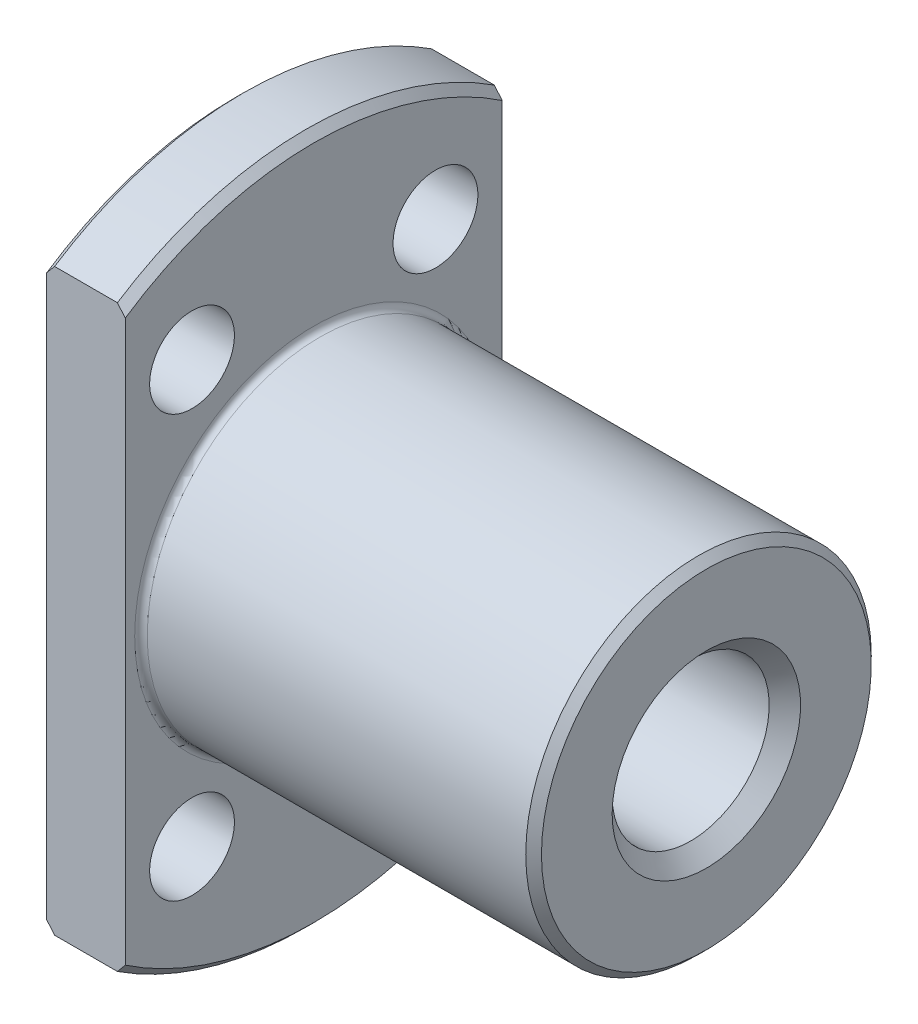
SolidWorks part; units mm, degrees
ref_plane "Front Plane" through (0, 0, 0) normal (0, 0, 1) x (1, 0, 0)
ref_plane "Top Plane" through (0, 0, 0) normal (0, 1, 0) x (1, 0, 0)
ref_plane "Right Plane" through (0, 0, 0) normal (1, 0, 0) x (0, 0, -1)
ref_plane "Plane1" through (0, 0, 0) normal (0, 0, 1) x (1, 0, 0)
sketch "Sketch1" plane through (0, 0, 0) normal (0, 0, 1) x (1, 0, 0)
  line L0 (0, 0) -> (0, 21.5)
  line L1 (0, 21.5) -> (0.5, 22)
  line L2 (0.5, 22) -> (4.5, 22)
  line L3 (4.5, 22) -> (5, 21.5)
  line L4 (5, 21.5) -> (5, 11.4)
  line L5 (5.4, 11) -> (29.5, 11)
  line L6 (29.5, 11) -> (30, 10.5)
  line L7 (30, 10.5) -> (30, 0)
  line L8 (30, 0) -> (0, 0)
  line L9 (30, 0) -> (0, 0) construction
  arc A0 (5, 11.4) -> (5.4, 11) centre (5.4, 11.4) ccw
revolve "Revolve1" add sketch "Sketch1" angle 360 about L9
ref_plane "Plane2" through (0, 0, 0) normal (0, 0, 1) x (1, 0, 0)
sketch "Sketch2" plane through (0, 0, 0) normal (0, 0, 1) x (1, 0, 0)
  line L0 (0, 0) -> (0, 6)
  line L1 (0, 6) -> (1, 5)
  line L2 (1, 5) -> (29, 5)
  line L3 (29, 5) -> (30, 6)
  line L4 (30, 6) -> (30, 0)
  line L5 (30, 0) -> (0, 0)
  line L6 (30, 0) -> (0, 0) construction
revolve "Cut-Revolve1" cut sketch "Sketch2" angle 360 about L6
cosmetic thread "Cosmetic Thread1" parameters "D1"=30, "D2"=12
ref_plane "Plane3" through (0, 0, 0) normal (1, 0, 0) x (0, 0, -1)
sketch "Sketch3" plane through (0, 0, 0) normal (1, 0, 0) x (0, 0, -1)
  line L0 (-24, -66) -> (24, -66)
  line L1 (24, -66) -> (24, 66)
  line L2 (24, 66) -> (-24, 66)
  line L3 (-24, 66) -> (-24, -66)
  line L4 (-12, -44) -> (12, -44)
  line L5 (12, -44) -> (12, 44)
  line L6 (12, 44) -> (-12, 44)
  line L7 (-12, 44) -> (-12, -44)
extrude "Cut-Extrude1" cut sketch "Sketch3" against normal blind 7.5 and the other way blind 7.5
ref_plane "Plane4" through (-0.5, 0, 0) normal (1, 0, 0) x (0, 0, -1)
sketch "Sketch4" plane through (-0.5, 0, 0) normal (1, 0, 0) x (0, 0, -1)
  circle A0 centre (-7.75, 13.4234) radius 2.7
extrude "Cut-Extrude2" cut sketch "Sketch4" along normal blind 6
ref_plane "Plane5" through (-0.5, 0, 0) normal (1, 0, 0) x (0, 0, -1)
sketch "Sketch5" plane through (-0.5, 0, 0) normal (1, 0, 0) x (0, 0, -1)
  circle A0 centre (-7.75, -13.4234) radius 2.7
extrude "Cut-Extrude3" cut sketch "Sketch5" along normal blind 6
ref_plane "Plane6" through (-0.5, 0, 0) normal (1, 0, 0) x (0, 0, -1)
sketch "Sketch6" plane through (-0.5, 0, 0) normal (1, 0, 0) x (0, 0, -1)
  circle A0 centre (7.75, -13.4234) radius 2.7
extrude "Cut-Extrude4" cut sketch "Sketch6" along normal blind 6
ref_plane "Plane7" through (-0.5, 0, 0) normal (1, 0, 0) x (0, 0, -1)
sketch "Sketch7" plane through (-0.5, 0, 0) normal (1, 0, 0) x (0, 0, -1)
  circle A0 centre (7.75, 13.4234) radius 2.7
extrude "Cut-Extrude5" cut sketch "Sketch7" along normal blind 6
